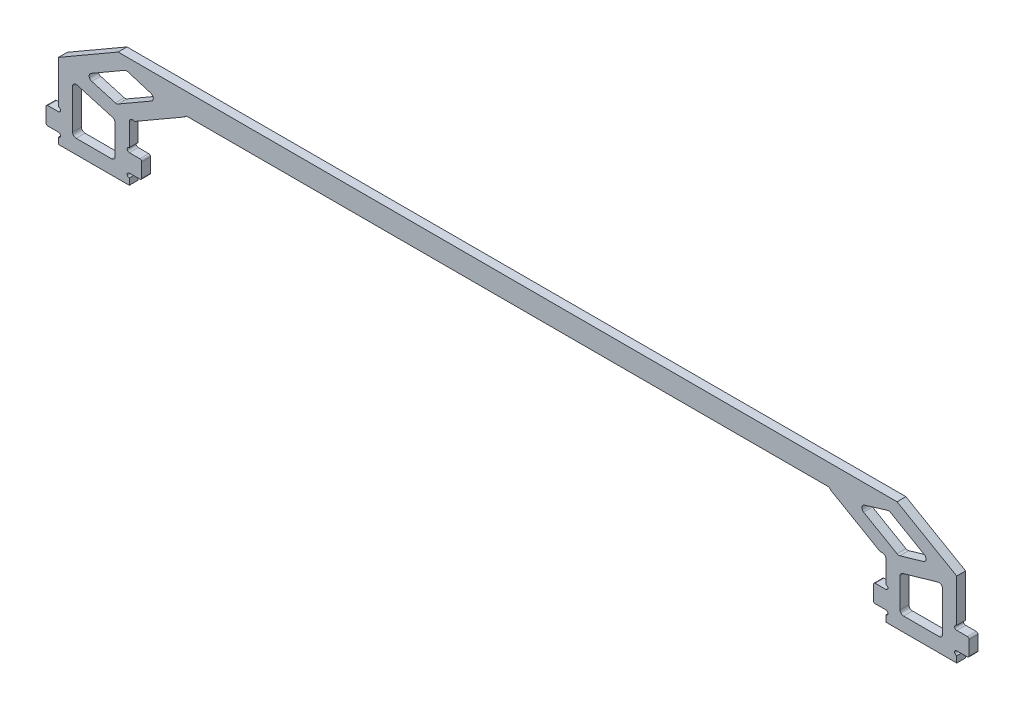
SolidWorks part; units mm, degrees
ref_plane "前视基准面" through (0, 0, 0) normal (0, 0, 1) x (1, 0, 0)
ref_plane "上视基准面" through (0, 0, 0) normal (0, 1, 0) x (1, 0, 0)
ref_plane "右视基准面" through (0, 0, 0) normal (1, 0, 0) x (0, 0, -1)
sketch "草图1" plane through (0, 0, 0) normal (0, 0, 1) x (1, 0, 0)
  line L0 (-126.75, 40) -> (-126.75, 0)
  line L1 (-126.75, 0) -> (-106.75, 0)
  line L2 (-106.75, 0) -> (-106.75, 15.5)
  line L3 (-90.2955, 25) -> (101.2652, 25)
  line L4 (101.2652, 25) -> (106.75, 15.5)
  line L5 (106.75, 15.5) -> (106.75, 0)
  line L6 (106.75, 0) -> (126.75, 0)
  line L7 (126.75, 0) -> (126.75, 40)
  line L9 (126.75, 40) -> (-126.75, 40)
  line L10 (-106.75, 0) -> (106.75, 0) construction
  line L11 (-106.75, 15.5) -> (-90.2955, 25)
  dimension "D1" = 253.5
  dimension "D2" = 20
  dimension "D3" = 15.5
  dimension "D4" = 25
  dimension "D5" = 60
  dimension "D6" = 40
  dimension "D7" = 30
extrude "凸台-拉伸1" add sketch "草图1" along normal mid plane 2.5
sketch "草图2" plane through (0, 0, 1.25) normal (0, 0, 1) x (1, 0, 0)
  line L0 (-106.75, 3) -> (-103.25, 3)
  line L1 (-106.75, 0) -> (-106.75, 15.5) construction
  line L2 (-103.25, 3) -> (-103.25, 8)
  line L3 (-103.25, 8) -> (-106.75, 8)
  line L4 (-106.75, 8) -> (-106.75, 3)
  line L5 (0, 0) -> (0, 25) construction
  line L6 (-90.2955, 25) -> (101.2652, 25) construction
  line L8 (-126.75, 0) -> (-106.75, 0) construction
  line L9 (103.25, 8) -> (106.75, 8)
  line L10 (103.25, 3) -> (103.25, 8)
  line L11 (106.75, 3) -> (103.25, 3)
  line L12 (106.75, 8) -> (106.75, 3)
  line L13 (-126.75, 40) -> (-126.75, 0) construction
  line L14 (-130.25, 8) -> (-126.75, 8)
  line L15 (-130.25, 8) -> (-130.25, 3)
  line L16 (-130.25, 3) -> (-126.75, 3)
  line L17 (-126.75, 8) -> (-126.75, 3)
  line L18 (130.25, 3) -> (126.75, 3)
  line L19 (126.75, 8) -> (126.75, 3)
  line L20 (130.25, 8) -> (126.75, 8)
  line L21 (130.25, 8) -> (130.25, 3)
  dimension "D1" = 5
  dimension "D2" = 3.5
  dimension "D3" = 3
extrude "凸台-拉伸2" add sketch "草图2" against normal blind 2.5
sketch "草图3" plane through (0, 0, 1.25) normal (0, 0, 1) x (1, 0, 0)
  line L0 (-106.75, 8) -> (-106.75, 15.5) construction
  line L1 (-106.75, 0) -> (-106.75, 3) construction
  line L2 (106.75, 15.5) -> (106.75, 8) construction
  line L3 (106.75, 3) -> (106.75, 0) construction
  line L4 (-126.75, 40) -> (-126.75, 8) construction
  line L5 (-126.75, 3) -> (-126.75, 0) construction
  line L6 (126.75, 8) -> (126.75, 40) construction
  line L7 (126.75, 0) -> (126.75, 3) construction
  circle A0 centre (-106.75, 8.6) radius 0.6
  circle A1 centre (-106.75, 2.4) radius 0.6
  circle A2 centre (106.75, 8.6) radius 0.6
  circle A3 centre (106.75, 2.4) radius 0.6
  circle A4 centre (-126.75, 8.6) radius 0.6
  circle A5 centre (-126.75, 2.4) radius 0.6
  circle A6 centre (126.75, 8.6) radius 0.6
  circle A7 centre (126.75, 2.4) radius 0.6
  dimension "D1" = 1.2
extrude "切除-拉伸1" cut sketch "草图3" against normal through all
fillet "圆角1" radius 0.5 8 edges at (103.25, 3, 0) (103.25, 8, 0) (130.25, 3, 0) (130.25, 8, 0) (-103.25, 3, 0) (-103.25, 8, 0) (-130.25, 8, 0) (-130.25, 3, 0)
sketch "草图4" plane through (0, 0, 1.25) normal (0, 0, 1) x (1, 0, 0)
  line L0 (-113.8986, 36) -> (-122.5186, 11.0148)
  line L1 (-122.5186, 11.0148) -> (-91.3673, 29)
  line L2 (-91.3673, 29) -> (91.3673, 29)
  line L3 (0, 29) -> (0, 36) construction
  line L4 (113.8986, 36) -> (-113.8986, 36)
  line L5 (-106.75, 15.5) -> (-90.2955, 25) construction
  line L6 (126.75, 40) -> (-126.75, 40) construction
  line L7 (-90.2955, 25) -> (101.2652, 25) construction
  line L8 (-116.75, 40) -> (-126.75, 11.0148)
  line L9 (-126.75, 40) -> (-126.75, 9.2) construction
  line L10 (-126.75, 11.0148) -> (-126.75, 40)
  line L11 (-126.75, 40) -> (-116.75, 40)
  line L12 (122.5186, 11.0148) -> (91.3673, 29)
  line L13 (113.8986, 36) -> (122.5186, 11.0148)
  line L14 (116.75, 40) -> (126.75, 11.0148)
  line L15 (126.75, 40) -> (116.75, 40)
  line L16 (126.75, 11.0148) -> (126.75, 40)
  dimension "D1" = 4
  dimension "D2" = 4
  dimension "D3" = 4
  dimension "D4" = 4
  dimension "D6" = 10
sketch "草图7" plane through (0, 0, 1.25) normal (0, 0, 1) x (1, 0, 0)
  line L0 (-126.75, 21.2735) -> (-94.3148, 40)
  line L1 (-126.75, 40) -> (-126.75, 9.2) construction
  line L2 (126.75, 40) -> (-126.75, 40) construction
  line L3 (-94.3148, 40) -> (-126.75, 40)
  line L4 (-126.75, 40) -> (-126.75, 21.2735)
  line L5 (-106.75, 15.5) -> (-90.2955, 25) construction
  line L9 (109.9254, 40) -> (126.75, 40)
  line L10 (126.75, 10.859) -> (109.9254, 40)
  line L11 (126.75, 40) -> (126.75, 10.859)
  line L12 (101.2652, 25) -> (106.75, 15.5) construction
  line L13 (126.75, 9.2) -> (126.75, 40) construction
  dimension "D1" = 15
  dimension "D2" = 15
extrude "切除-拉伸3" cut sketch "草图7" against normal through all
sketch "草图10" plane through (0, 0, 1.25) normal (0, 0, 1) x (1, 0, 0)
  line L0 (-109.9032, 31) -> (59.1996, 31)
  line L2 (59.1996, 31) -> (69.9254, 40)
  line L4 (-109.9032, 31) -> (-94.3148, 40)
  line L5 (-94.3148, 40) -> (69.9254, 40)
  line L6 (-90.2955, 25) -> (101.2652, 25) construction
  line L8 (-126.75, 21.2735) -> (-94.3148, 40) construction
  line L9 (109.9254, 40) -> (-94.3148, 40) construction
  dimension "D1" = 6
  dimension "D2" = 40
  dimension "D3" = 40
extrude "切除-拉伸5" cut sketch "草图10" against normal through all
sketch "草图11" plane through (0, 0, 1.25) normal (0, 0, 1) x (1, 0, 0)
  line L0 (-109.9032, 31) -> (-90.2955, 25) construction
  line L1 (-126.75, 21.2735) -> (-106.75, 15.5) construction
  line L9 (-107.6342, 27.6912) -> (-119.6139, 20.7747)
  line L10 (-122.75, 17.5167) -> (-122.75, 4)
  line L11 (-122.75, 4) -> (-110.75, 4)
  line L12 (-110.75, 4) -> (-110.75, 14.0526)
  line L13 (-110.2806, 18.0804) -> (-98.4839, 24.8912)
  line L15 (-106.75, 15.5) -> (-90.2955, 25) construction
  line L16 (-126.75, 21.2735) -> (-109.9032, 31) construction
  line L17 (-126.75, 0) -> (-106.75, 0) construction
  line L18 (-107.6342, 27.6912) -> (-98.4839, 24.8912)
  line L19 (-122.75, 17.5167) -> (-110.75, 14.0526)
  line L20 (-110.6347, 28.6094) -> (-91.027, 22.6094) construction
  line L21 (-119.6139, 20.7747) -> (-110.2806, 18.0804)
  line L22 (-126.334, 22.7147) -> (-106.334, 16.9412) construction
  line L23 (-127.4434, 18.8716) -> (-107.4434, 13.0981) construction
  line L24 (-126.75, 21.2735) -> (-126.75, 9.2) construction
  line L25 (-106.75, 9.2) -> (-106.75, 15.5) construction
  line L26 (0, 25) -> (0, 0) construction
  line L37 (122.75, 10.2473) -> (122.75, 4)
  line L38 (122.75, 4) -> (110.75, 4)
  line L39 (110.75, 4) -> (110.75, 13.0319)
  line L40 (126.75, 10.859) -> (106.75, 15.5) construction
  line L41 (-90.2955, 25) -> (101.2652, 25) construction
  line L42 (122.75, 10.2473) -> (110.75, 13.0319)
  line L43 (122.0017, 10.421) -> (110.3086, 13.1344) construction
  line L44 (122.3407, 11.8822) -> (110.6477, 14.5955) construction
  line L45 (101.2652, 25) -> (106.75, 15.5) construction
  line L46 (126.75, 9.2) -> (126.75, 10.859) construction
  dimension "D1" = 4
  dimension "D2" = 4
  dimension "D3" = 4
  dimension "D6" = 4
  dimension "D7" = 4
  dimension "D8" = 1.5
  dimension "D4" = 2.5
  dimension "D5" = 1.5
extrude "切除-拉伸6" cut sketch "草图11" against normal through all
fillet "圆角4" radius 1 12 edges at (122.75, 4, 0) (110.75, 4, 0) (-122.75, 17.5167, 0) (-110.75, 4, 0) (-122.75, 4, 0) (-110.75, 14.0526, 0) (-110.2806, 18.0804, 0) (-119.6139, 20.7747, 0) (-107.6342, 27.6912, 0) (-98.4839, 24.8912, 0) (122.75, 10.2473, 0) (110.75, 13.0319, 0)
sketch "草图12" plane through (0, 0, 1.25) normal (0, 0, 1) x (1, 0, 0)
  line L0 (-90.2955, 25) -> (101.2652, 25) construction
  line L1 (-106.75, 9.2) -> (-106.75, 15.5) construction
  line L2 (-109.9032, 31) -> (59.1996, 31) construction
  line L3 (106.75, 15.5) -> (106.75, 9.2) construction
  circle A0 centre (-90.2955, 24) radius 1
  circle A1 centre (-105.75, 15.5) radius 1
  circle A2 centre (59.1996, 32) radius 1
  circle A5 centre (101.2652, 24) radius 1
  circle A6 centre (105.75, 15.5) radius 1
  dimension "D1" = 2
extrude "切除-拉伸7" cut sketch "草图12" against normal through all
sketch "草图13" plane through (0, 0, 1.25) normal (0, 0, 1) x (1, 0, 0)
  line L0 (0, 52.4467) -> (0, 0)
  line L1 (0, 0) -> (157.6635, 0)
  line L2 (157.6635, 0) -> (157.6635, 52.4467)
  line L3 (157.6635, 52.4467) -> (0, 52.4467)
extrude "切除-拉伸8" cut sketch "草图13" against normal through all
mirror "镜向2" about plane through (0, 52.4467, -1.25) normal (-1, 0, 0) of bodies 113
